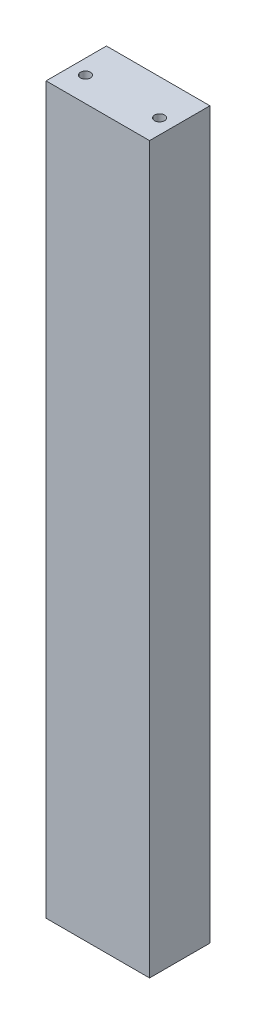
SolidWorks part; units mm, degrees
material "6061-T6 (SS)"
ref_plane "Front Plane" through (0, 0, 0) normal (0, 0, 1) x (1, 0, 0)
ref_plane "Top Plane" through (0, 0, 0) normal (0, 1, 0) x (1, 0, 0)
ref_plane "Right Plane" through (0, 0, 0) normal (1, 0, 0) x (0, 0, -1)
sketch "Sketch1" plane through (0, 0, 0) normal (0, 1, 0) x (1, 0, 0)
  line L1 (0, 0) -> (41.91, 0)
  line L2 (0, 0) -> (0, 24.4475)
  line L3 (0, 24.4475) -> (41.91, 24.4475)
  line L4 (41.91, 0) -> (41.91, 24.4475)
  dimension "D1" = 24.4475
  dimension "D2" = 41.91
extrude "Boss-Extrude1" add sketch "Sketch1" along normal blind 293.6875
hole_wizard "#10-32 Tapped Hole1" positions "Sketch2" profile "Sketch3" tap size "#10-32" standard "ANSI Inch"
sketch "Sketch2" plane through (0, 293.6875, 0) normal (0, 1, 0) x (-1, 0, 0)
  line L0 (-5.955, -10) -> (-35.955, -10) construction
  line L2 (0, 0) -> (-41.91, 0) construction
  point P0 (-5.955, -10)
  point P2 (-35.955, -10)
  point P15 (-20.955, -10)
  point P16 (-20.955, 0)
  dimension "D1" = 30
  dimension "D2" = 10
sketch "Sketch3" plane through (5.955, 293.6875, -10) normal (1, 0, 0) x (0, 0, 1)
  line L0 (0, 0) -> (0, 20.0093)
  line L1 (0, 20.0093) -> (2.0193, 18.796)
  line L2 (2.0193, 18.796) -> (2.0193, 0)
  line L5 (2.0193, 0) -> (0, 0)
  line L10 (0, 20.0093) -> (-2.0193, 18.796) construction
  line L11 (0, -6.35) -> (0, 107.95) construction
  dimension "Tap Drill Dia." = 4.0386
  dimension "Tap Drill Depth" = 18.796
  dimension "Drill Angle" = 118
cosmetic thread "Hole Thread1"
cosmetic thread "Hole Thread2"
hole_wizard "#10-32 Tapped Hole3" positions "Sketch9" profile "Sketch11" tap size "#10-32" standard "ANSI Inch"
sketch "Sketch9" plane through (51.0034, 0, 2.458) normal (0, -1, 0) x (1, 0, 0)
  line L0 (-15.0484, -12.458) -> (-45.0484, -12.458) construction
  line L3 (-51.0034, -2.458) -> (-9.0934, -2.458) construction
  point P0 (-15.0484, -12.458)
  point P2 (-45.0484, -12.458)
  point P15 (-30.0484, -12.458)
  point P19 (-30.0484, -2.458)
  dimension "D1" = 30
  dimension "D2" = 10
sketch "Sketch11" plane through (35.955, 0, -10) normal (1, 0, 0) x (0, 0, -1)
  line L0 (0, 0) -> (0, 20.0093)
  line L1 (0, 20.0093) -> (2.0193, 18.796)
  line L2 (2.0193, 18.796) -> (2.0193, 0)
  line L5 (2.0193, 0) -> (0, 0)
  line L10 (0, 20.0093) -> (-2.0193, 18.796) construction
  line L11 (0, -6.35) -> (0, 107.95) construction
  dimension "Tap Drill Dia." = 4.0386
  dimension "Tap Drill Depth" = 18.796
  dimension "Drill Angle" = 118
cosmetic thread "Hole Thread5"
cosmetic thread "Hole Thread7"
